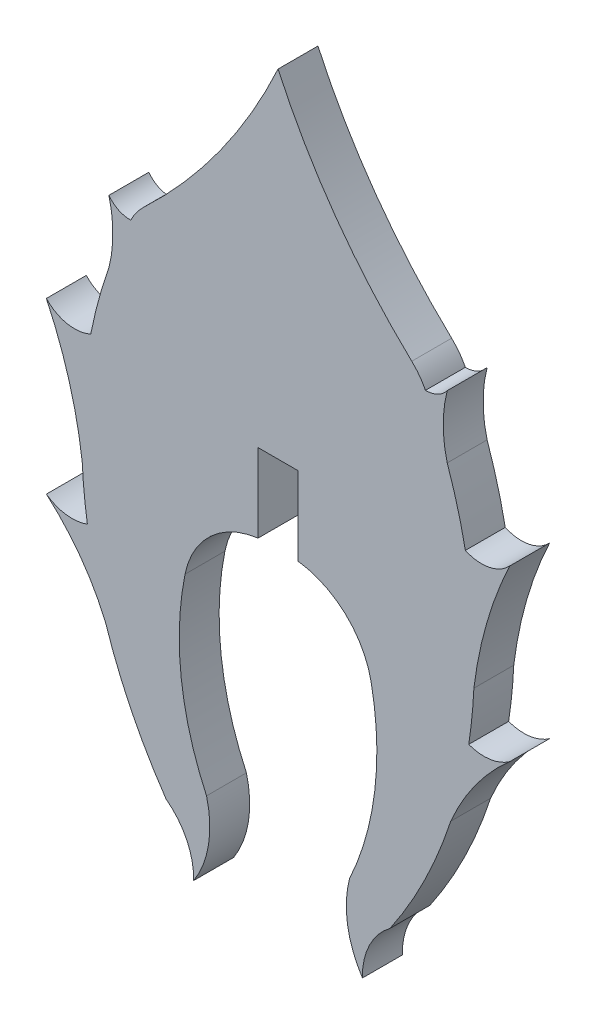
SolidWorks part; units mm, degrees
ref_plane "Front Plane" through (0, 0, 0) normal (0, 0, 1) x (1, 0, 0)
ref_plane "Top Plane" through (0, 0, 0) normal (0, 1, 0) x (1, 0, 0)
ref_plane "Right Plane" through (0, 0, 0) normal (1, 0, 0) x (0, 0, -1)
sketch "Sketch1" plane through (0, 0, 0) normal (0, 0, 1) x (1, 0, 0)
  line L0 (-0.7654, -0.5031) -> (-0.765, 2.4922)
  line L1 (-0.765, 2.4922) -> (0.761, 2.4922)
  line L2 (0.761, 2.4922) -> (0.761, -0.5031)
  arc A0 (5.1062, 8.2858) -> (5.6301, 7.5841) centre (3.3634, 6.438) cw
  arc A1 (-3.226, -13.0637) -> (-4.2797, -10.8949) centre (-5.8563, -13.0013) ccw
  arc A2 (-2.7347, -10.0151) -> (-3.226, -13.0637) centre (-6.4229, -10.9847) cw
  arc A3 (-7.2873, -3.3042) -> (-7.4835, -1.3469) centre (10.8885, -0.4937) cw
  arc A4 (-7.1586, 3.0503) -> (-6.4649, 5.5987) centre (10.8885, -0.4937) cw
  arc A5 (3.552, -3.0908) -> (0.761, -0.5031) centre (0.3592, -3.7354) ccw
  arc A6 (2.7307, -10.0151) -> (3.552, -3.0908) centre (-7.3937, -5.3035) ccw
  arc A7 (-5.1102, 8.2858) -> (-0.002, 15.3992) centre (-20.8669, 24.9915) ccw
  arc A8 (4.2757, -10.8949) -> (6.5945, -6.1911) centre (-10.8925, -0.4937) ccw
  arc A9 (6.5945, -6.1911) -> (8.8498, -3.0908) centre (14.4492, -9.5344) cw
  arc A10 (8.8498, -3.0908) -> (7.2833, -3.3042) centre (7.8656, -1.722) cw
  arc A11 (7.4795, -1.3469) -> (8.8498, 3.3832) centre (22.7982, -3.2213) cw
  arc A12 (8.8498, 3.3832) -> (7.1546, 3.0503) centre (7.7698, 4.4003) cw
  arc A13 (6.4609, 5.5987) -> (6.4609, 7.9901) centre (11.0559, 6.7944) cw
  arc A14 (6.4609, 7.9901) -> (5.6301, 7.5841) centre (5.6465, 8.6035) cw
  arc A15 (5.1062, 8.2858) -> (-0.002, 15.3992) centre (20.8629, 24.9915) cw
  arc A16 (-6.4649, 7.9901) -> (-5.6341, 7.5841) centre (-5.6505, 8.6035) ccw
  arc A17 (7.1546, 3.0503) -> (6.4609, 5.5987) centre (-10.8925, -0.4937) ccw
  arc A18 (7.2833, -3.3042) -> (7.4795, -1.3469) centre (-10.8925, -0.4937) ccw
  arc A19 (2.7307, -10.0151) -> (3.222, -13.0637) centre (6.4189, -10.9847) ccw
  arc A20 (3.222, -13.0637) -> (4.2757, -10.8949) centre (5.8523, -13.0013) cw
  arc A21 (-6.4649, 5.5987) -> (-6.4649, 7.9901) centre (-11.0599, 6.7944) ccw
  arc A22 (-8.8538, 3.3832) -> (-7.1586, 3.0503) centre (-7.7738, 4.4003) ccw
  arc A23 (-7.4835, -1.3469) -> (-8.8538, 3.3832) centre (-22.8022, -3.2213) ccw
  arc A24 (-8.8538, -3.0908) -> (-7.2873, -3.3042) centre (-7.8696, -1.722) ccw
  arc A25 (-6.5985, -6.1911) -> (-8.8538, -3.0908) centre (-14.4532, -9.5344) ccw
  arc A26 (-4.2797, -10.8949) -> (-6.5985, -6.1911) centre (10.8885, -0.4937) cw
  arc A27 (-2.7347, -10.0151) -> (-3.556, -3.0908) centre (7.3897, -5.3035) cw
  arc A28 (-3.556, -3.0908) -> (-0.7654, -0.5031) centre (-0.3632, -3.7354) cw
  arc A29 (-5.1102, 8.2858) -> (-5.6341, 7.5841) centre (-3.3674, 6.438) ccw
extrude "Boss-Extrude2" add sketch "Sketch1" along normal blind 1.524
